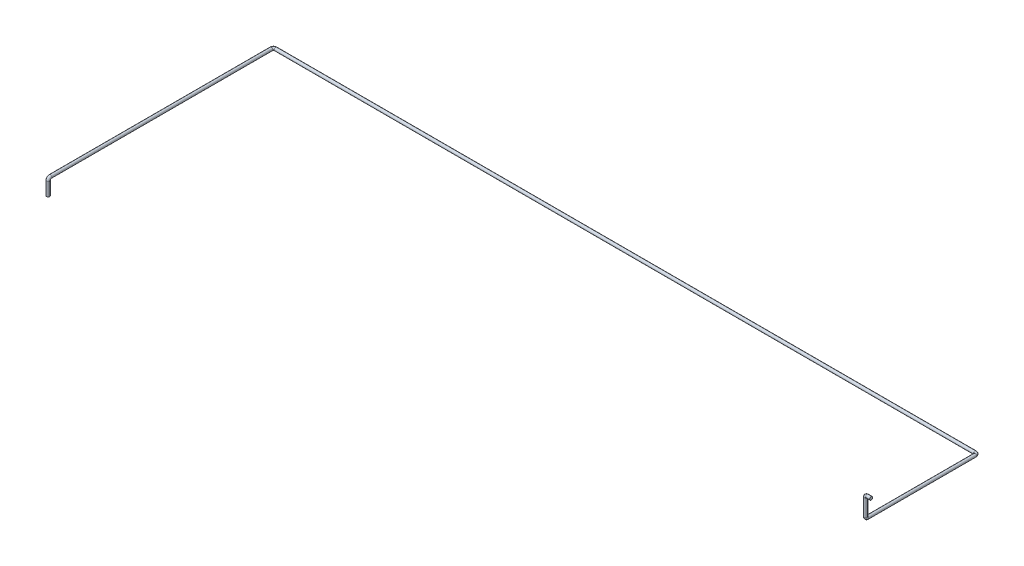
SolidWorks part; units mm, degrees
ref_plane "Alzado" through (0, 0, 0) normal (0, 0, 1) x (1, 0, 0)
ref_plane "Planta" through (0, 0, 0) normal (0, 1, 0) x (1, 0, 0)
ref_plane "Vista lateral" through (0, 0, 0) normal (1, 0, 0) x (0, 0, -1)
sketch3d "Croquis3D1"
  line L0 (0, 0, 0) -> (-36, 0, 0)
  line L1 (-50, -14, 0) -> (-50, -166, 0)
  line L2 (-50, -180, -14) -> (-50, -180, -980)
  line L3 (-70, -180, -1000) -> (-6340, -180, -1000)
  line L4 (-6360, -180, -980) -> (-6360, -180, 1000)
  line L5 (-6360, -200, 1020) -> (-6360, -320, 1020)
  arc A0 (-50, -166, 0) -> (-50, -180, -14) centre (-50, -166, -14) ccw
  arc A1 (-36, 0, 0) -> (-50, -14, 0) centre (-36, -14, 0) ccw
  arc A2 (-6360, -180, 1000) -> (-6360, -200, 1020) centre (-6360, -200, 1000) ccw
  arc A3 (-6340, -180, -1000) -> (-6360, -180, -980) centre (-6340, -180, -980) ccw
  arc A4 (-50, -180, -980) -> (-70, -180, -1000) centre (-70, -180, -980) ccw
  point P10 (-50, -180, 0)
  point P11 (-36, -166, -14)
  point P14 (-50, 0, 0)
  point P15 (-36, -14, 14)
  point P18 (-6360, -180, 1020)
  point P19 (-6340, -200, 1000)
  point P22 (-6360, -180, -1000)
  point P23 (-6340, -160, -980)
  point P26 (-50, -180, -1000)
  point P27 (-70, -160, -980)
  dimension "D7" = 14
  dimension "D8" = 20
  dimension "D1" = 50
  dimension "D2" = 180
  dimension "D3" = 1000
  dimension "D4" = 6310
  dimension "D5" = 2020
  dimension "D6" = 140
sketch "Croquis1" plane through (0, 0, 0) normal (1, 0, 0) x (0, 0, -1)
  circle A0 centre (0, 0) radius 13.7
  dimension "D1" = 27.4
sweep "Barrer1" add profiles "Croquis1" path "Croquis3D1"
